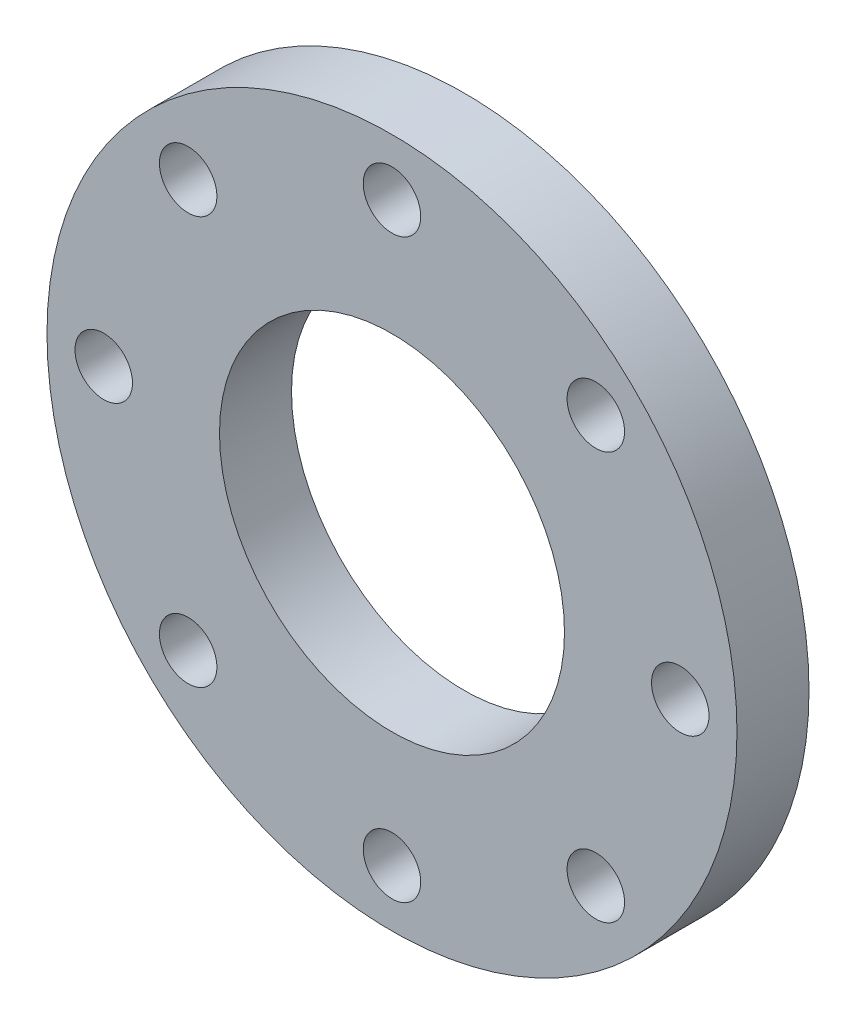
SolidWorks part; units mm, degrees
material "Alloy Steel"
ref_plane "Front Plane" through (0, 0, 0) normal (0, 0, 1) x (1, 0, 0)
ref_plane "Top Plane" through (0, 0, 0) normal (0, 1, 0) x (1, 0, 0)
ref_plane "Right Plane" through (0, 0, 0) normal (1, 0, 0) x (0, 0, -1)
sketch "Sketch19" plane through (0, 0, 0) normal (0, 0, 1) x (1, 0, 0)
  line L0 (0, 0) -> (0, -72795.8344) construction
  line L1 (0, 0) -> (-72795.8344, 0) construction
  circle A0 centre (0, 0) radius 57
  circle A1 centre (0, 0) radius 114
  circle A2 centre (0, 0) radius 95.25 construction
  circle A3 centre (0, 95.25) radius 9.5
  circle A4 centre (67.3519, 67.3519) radius 9.5
  circle A5 centre (95.25, 0) radius 9.5
  circle A6 centre (67.3519, -67.3519) radius 9.5
  circle A7 centre (0, -95.25) radius 9.5
  circle A8 centre (-67.3519, -67.3519) radius 9.5
  circle A9 centre (-95.25, 0) radius 9.5
  circle A10 centre (-67.3519, 67.3519) radius 9.5
  point P27 (0, 0)
  dimension "D1" = 114
  dimension "D2" = 190.5
  dimension "D3" = 228
  dimension "D4" = 19
  dimension "D5" = 8
extrude "Boss-Extrude1" add sketch "Sketch19" along normal blind 23.8
